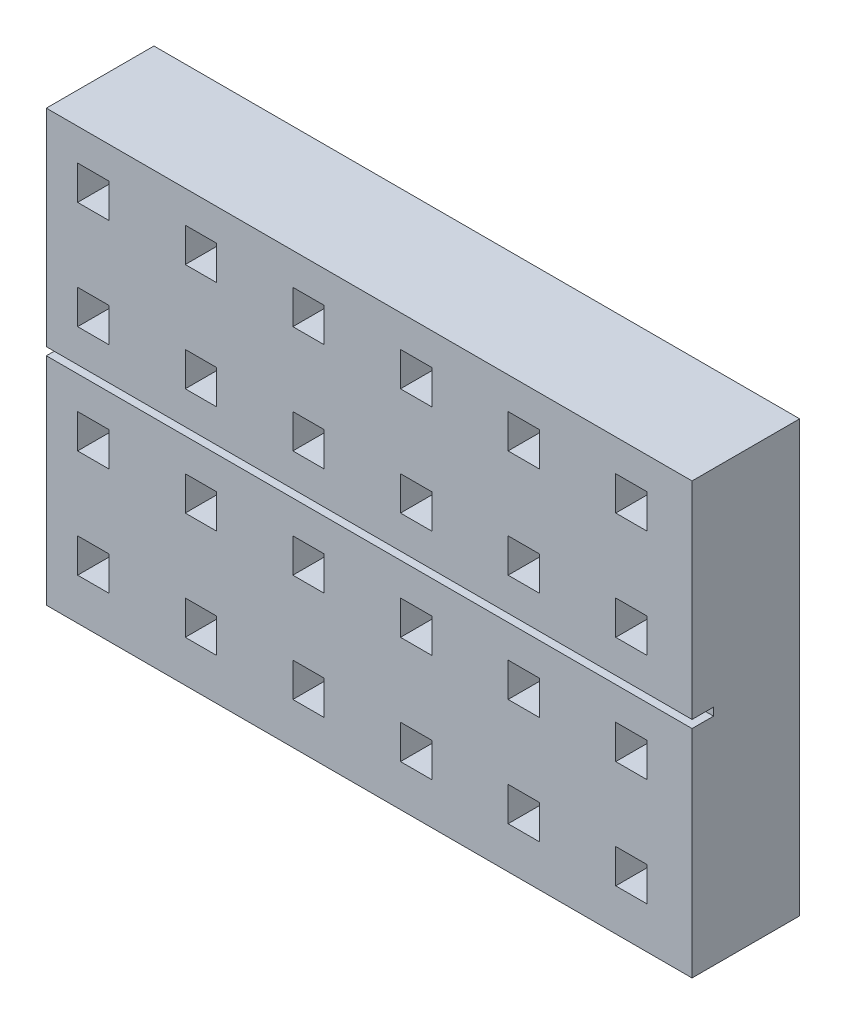
SolidWorks part; units mm, degrees
ref_plane "Front Plane" through (0, 0, 0) normal (0, 0, 1) x (1, 0, 0)
ref_plane "Top Plane" through (0, 0, 0) normal (0, 1, 0) x (1, 0, 0)
ref_plane "Right Plane" through (0, 0, 0) normal (1, 0, 0) x (0, 0, -1)
sketch "Sketch1" plane through (0, 0, 0) normal (0, 0, 1) x (1, 0, 0)
  line L1 (-28.0851, 26.4894) -> (31.9149, 26.4894)
  line L2 (-28.0851, 26.4894) -> (-28.0851, -13.5106)
  line L3 (-28.0851, -13.5106) -> (31.9149, -13.5106)
  line L4 (31.9149, 26.4894) -> (31.9149, -13.5106)
  dimension "D1" = 60
  dimension "D2" = 40
extrude "Boss-Extrude1" add sketch "Sketch1" along normal blind 10
sketch "Sketch2" plane through (0, 0, 10) normal (0, 0, 1) x (1, 0, 0)
  line L0 (-15.1765, 23.5265) -> (-15.1765, 20.3583)
  line L1 (-25.1765, 23.5265) -> (-22.2669, 23.5265)
  line L2 (-25.1765, 23.5265) -> (-25.1765, 20.3583)
  line L3 (-25.1765, 20.3583) -> (-22.2669, 20.3583)
  line L4 (-22.2669, 23.5265) -> (-22.2669, 20.3583)
  line L5 (-15.1765, 23.5265) -> (-12.2669, 23.5265)
  line L6 (-12.2669, 23.5265) -> (-12.2669, 20.3583)
  line L7 (-15.1765, 20.3583) -> (-12.2669, 20.3583)
  line L8 (-5.1765, 23.5265) -> (-5.1765, 20.3583)
  line L9 (-5.1765, 23.5265) -> (-2.2669, 23.5265)
  line L10 (-2.2669, 23.5265) -> (-2.2669, 20.3583)
  line L11 (-5.1765, 20.3583) -> (-2.2669, 20.3583)
  line L12 (4.8235, 23.5265) -> (4.8235, 20.3583)
  line L13 (4.8235, 23.5265) -> (7.7331, 23.5265)
  line L14 (7.7331, 23.5265) -> (7.7331, 20.3583)
  line L15 (4.8235, 20.3583) -> (7.7331, 20.3583)
  line L16 (14.8235, 23.5265) -> (14.8235, 20.3583)
  line L17 (14.8235, 23.5265) -> (17.7331, 23.5265)
  line L18 (17.7331, 23.5265) -> (17.7331, 20.3583)
  line L19 (14.8235, 20.3583) -> (17.7331, 20.3583)
  line L20 (24.8235, 23.5265) -> (24.8235, 20.3583)
  line L21 (24.8235, 23.5265) -> (27.7331, 23.5265)
  line L22 (27.7331, 23.5265) -> (27.7331, 20.3583)
  line L23 (24.8235, 20.3583) -> (27.7331, 20.3583)
  line L24 (-15.1765, 13.5265) -> (-15.1765, 10.3583)
  line L25 (-15.1765, 13.5265) -> (-12.2669, 13.5265)
  line L26 (-12.2669, 13.5265) -> (-12.2669, 10.3583)
  line L27 (-15.1765, 10.3583) -> (-12.2669, 10.3583)
  line L28 (-5.1765, 13.5265) -> (-5.1765, 10.3583)
  line L29 (-5.1765, 13.5265) -> (-2.2669, 13.5265)
  line L30 (-2.2669, 13.5265) -> (-2.2669, 10.3583)
  line L31 (-5.1765, 10.3583) -> (-2.2669, 10.3583)
  line L32 (4.8235, 13.5265) -> (4.8235, 10.3583)
  line L33 (4.8235, 13.5265) -> (7.7331, 13.5265)
  line L34 (7.7331, 13.5265) -> (7.7331, 10.3583)
  line L35 (4.8235, 10.3583) -> (7.7331, 10.3583)
  line L36 (14.8235, 13.5265) -> (14.8235, 10.3583)
  line L37 (14.8235, 13.5265) -> (17.7331, 13.5265)
  line L38 (17.7331, 13.5265) -> (17.7331, 10.3583)
  line L39 (14.8235, 10.3583) -> (17.7331, 10.3583)
  line L40 (24.8235, 13.5265) -> (24.8235, 10.3583)
  line L41 (24.8235, 13.5265) -> (27.7331, 13.5265)
  line L42 (27.7331, 13.5265) -> (27.7331, 10.3583)
  line L43 (24.8235, 10.3583) -> (27.7331, 10.3583)
  line L44 (-15.1765, 3.5265) -> (-15.1765, 0.3583)
  line L45 (-15.1765, 3.5265) -> (-12.2669, 3.5265)
  line L46 (-12.2669, 3.5265) -> (-12.2669, 0.3583)
  line L47 (-15.1765, 0.3583) -> (-12.2669, 0.3583)
  line L48 (-5.1765, 3.5265) -> (-5.1765, 0.3583)
  line L49 (-5.1765, 3.5265) -> (-2.2669, 3.5265)
  line L50 (-2.2669, 3.5265) -> (-2.2669, 0.3583)
  line L51 (-5.1765, 0.3583) -> (-2.2669, 0.3583)
  line L52 (4.8235, 3.5265) -> (4.8235, 0.3583)
  line L53 (4.8235, 3.5265) -> (7.7331, 3.5265)
  line L54 (7.7331, 3.5265) -> (7.7331, 0.3583)
  line L55 (4.8235, 0.3583) -> (7.7331, 0.3583)
  line L56 (14.8235, 3.5265) -> (14.8235, 0.3583)
  line L57 (14.8235, 3.5265) -> (17.7331, 3.5265)
  line L58 (17.7331, 3.5265) -> (17.7331, 0.3583)
  line L59 (14.8235, 0.3583) -> (17.7331, 0.3583)
  line L60 (24.8235, 3.5265) -> (24.8235, 0.3583)
  line L61 (24.8235, 3.5265) -> (27.7331, 3.5265)
  line L62 (27.7331, 3.5265) -> (27.7331, 0.3583)
  line L63 (24.8235, 0.3583) -> (27.7331, 0.3583)
  line L64 (-15.1765, -6.4735) -> (-15.1765, -9.6417)
  line L65 (-15.1765, -6.4735) -> (-12.2669, -6.4735)
  line L66 (-12.2669, -6.4735) -> (-12.2669, -9.6417)
  line L67 (-15.1765, -9.6417) -> (-12.2669, -9.6417)
  line L68 (-5.1765, -6.4735) -> (-5.1765, -9.6417)
  line L69 (-5.1765, -6.4735) -> (-2.2669, -6.4735)
  line L70 (-2.2669, -6.4735) -> (-2.2669, -9.6417)
  line L71 (-5.1765, -9.6417) -> (-2.2669, -9.6417)
  line L72 (4.8235, -6.4735) -> (4.8235, -9.6417)
  line L73 (4.8235, -6.4735) -> (7.7331, -6.4735)
  line L74 (7.7331, -6.4735) -> (7.7331, -9.6417)
  line L75 (4.8235, -9.6417) -> (7.7331, -9.6417)
  line L76 (14.8235, -6.4735) -> (14.8235, -9.6417)
  line L77 (14.8235, -6.4735) -> (17.7331, -6.4735)
  line L78 (17.7331, -6.4735) -> (17.7331, -9.6417)
  line L79 (14.8235, -9.6417) -> (17.7331, -9.6417)
  line L80 (24.8235, -6.4735) -> (24.8235, -9.6417)
  line L81 (24.8235, -6.4735) -> (27.7331, -6.4735)
  line L82 (27.7331, -6.4735) -> (27.7331, -9.6417)
  line L83 (24.8235, -9.6417) -> (27.7331, -9.6417)
  line L84 (-25.1765, 13.5265) -> (-25.1765, 10.3583)
  line L85 (-25.1765, 13.5265) -> (-22.2669, 13.5265)
  line L86 (-22.2669, 13.5265) -> (-22.2669, 10.3583)
  line L87 (-25.1765, 10.3583) -> (-22.2669, 10.3583)
  line L88 (-25.1765, 3.5265) -> (-25.1765, 0.3583)
  line L89 (-25.1765, 3.5265) -> (-22.2669, 3.5265)
  line L90 (-22.2669, 3.5265) -> (-22.2669, 0.3583)
  line L91 (-25.1765, 0.3583) -> (-22.2669, 0.3583)
  line L92 (-25.1765, -6.4735) -> (-25.1765, -9.6417)
  line L93 (-25.1765, -6.4735) -> (-22.2669, -6.4735)
  line L94 (-22.2669, -6.4735) -> (-22.2669, -9.6417)
  line L95 (-25.1765, -9.6417) -> (-22.2669, -9.6417)
  dimension "D1" = 6
  dimension "D2" = 4
extrude "Cut-Extrude1" cut sketch "Sketch2" against normal blind 10
sketch "Sketch3" plane through (0, 0, 10) normal (0, 0, 1) x (1, 0, 0)
  line L1 (-28.9281, 7.2926) -> (32.8195, 7.2926)
  line L2 (-28.9281, 7.2926) -> (-28.9281, 6.5631)
  line L3 (-28.9281, 6.5631) -> (32.8195, 6.5631)
  line L4 (32.8195, 7.2926) -> (32.8195, 6.5631)
extrude "Cut-Extrude2" cut sketch "Sketch3" against normal blind 2
